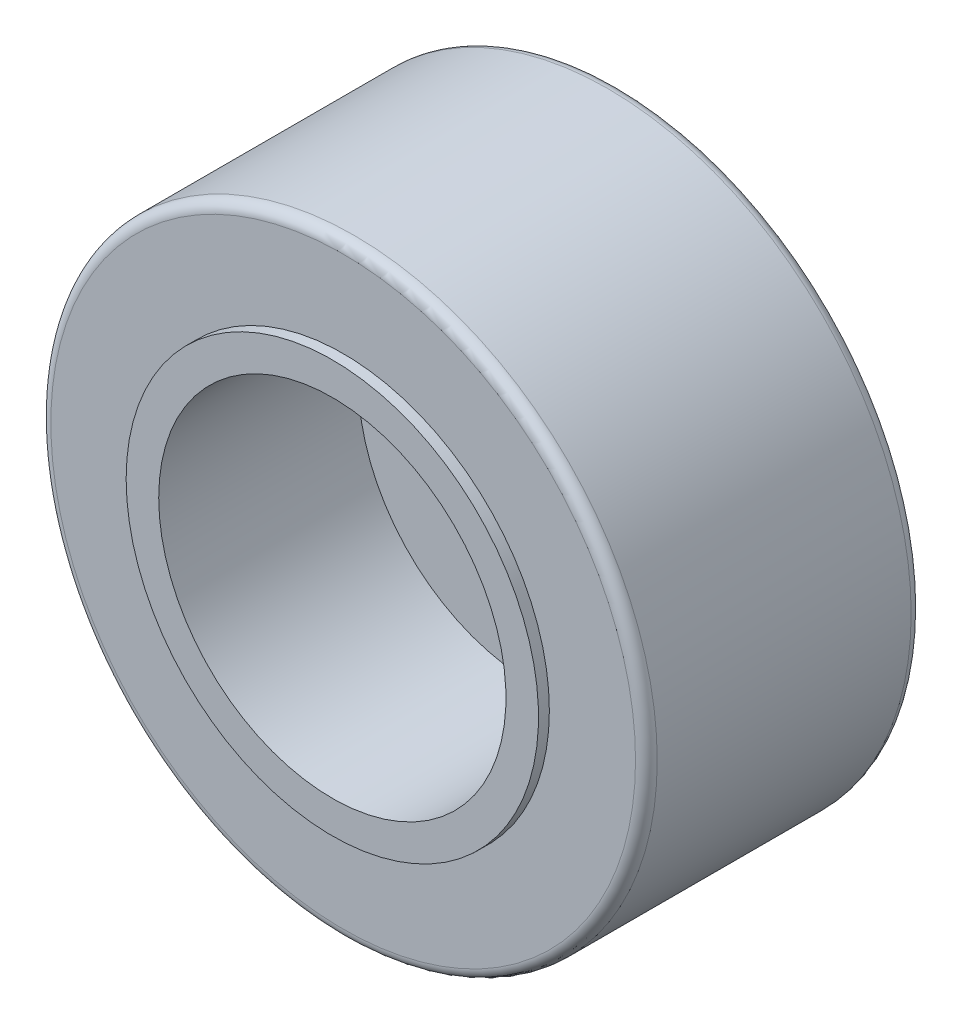
SolidWorks part; units mm, degrees
ref_plane "Front Plane" through (0, 0, 0) normal (0, 0, 1) x (1, 0, 0)
ref_plane "Top Plane" through (0, 0, 0) normal (0, 1, 0) x (1, 0, 0)
ref_plane "Right Plane" through (0, 0, 0) normal (1, 0, 0) x (0, 0, -1)
sketch "Sketch1" plane through (0, 0, 0) normal (0, 0, 1) x (1, 0, 0)
  circle A0 centre (0, 0) radius 8.5
  circle A1 centre (0, 0) radius 13.97
  dimension "D1" = 27.94
  dimension "D2" = 17
extrude "Boss-Extrude1" add sketch "Sketch1" along normal blind 12.7
fillet "Fillet1" radius 0.5 2 edges at (13.97, 0, 0) (13.97, 0, 12.7)
sketch "Sketch2" plane through (0, 0, 0) normal (1, 0, 0) x (0, 0, -1)
  line L0 (0, 0) -> (-12.7, 0) construction
  line L1 (-12.7, 13.47) -> (-12.7, -13.47) construction
  line L3 (0, 8.5) -> (0, -8.5) construction
  line L4 (0, 13.97) -> (0, -13.97) construction
  line L5 (0, 8.5) -> (-12.7, 8.5)
  line L6 (-12.7, 8.5) -> (-12.7, -8.5) construction
  line L7 (-12.7, 8.5) -> (-12.7, 9.5)
  line L8 (-12.7, 9.5) -> (-13.2, 9.5)
  line L9 (-13.2, 9.5) -> (-13.2, 8)
  line L10 (-13.2, 8) -> (-4, 8)
  line L11 (-4, 8) -> (-4, 1.5)
  line L14 (-4, 1.5) -> (0.5, 1.5)
  line L15 (-12.7, 8.5) -> (-12.7, -8.5)
  line L16 (-12.7, 8.5) -> (-12.7, -8.5) construction
  line L18 (0, 8.5) -> (0, 9.5)
  line L19 (0, -13.47) -> (0, 13.47) construction
  line L20 (0, 9.5) -> (0.5, 9.5)
  line L21 (0.5, 9.5) -> (0.5, 1.5)
  dimension "D1" = 0.5
  dimension "D2" = 0.5
  dimension "D3" = 0.5
  dimension "D4" = 0
  dimension "D5" = 1
  dimension "D6" = 1.5
  dimension "D7" = 4
revolve "Revolve1" add sketch "Sketch2" angle 360 about L0
ref_plane "Plane1" through (0, -13.97, 0) normal (0, -1, 0) x (-1, 0, 0)
